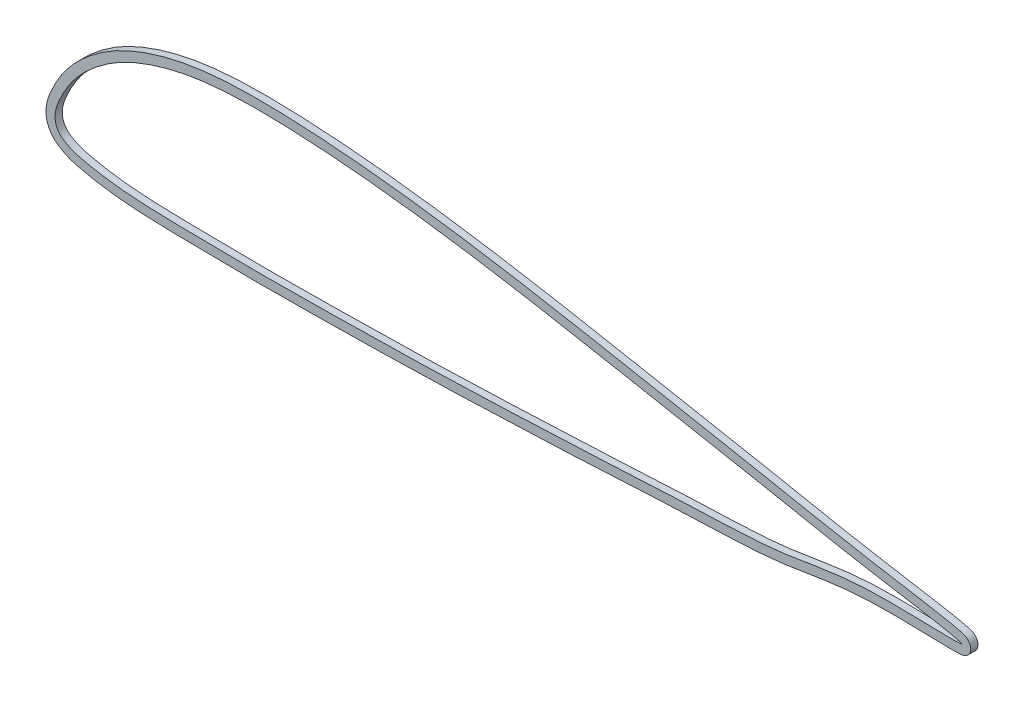
SolidWorks part; units mm, degrees
ref_plane "Front Plane" through (0, 0, 0) normal (0, 0, 1) x (1, 0, 0)
ref_plane "Top Plane" through (0, 0, 0) normal (0, 1, 0) x (1, 0, 0)
ref_plane "Right Plane" through (0, 0, 0) normal (1, 0, 0) x (0, 0, -1)
sketch "Sketch11" plane through (0, 0, 0) normal (0, 0, 1) x (1, 0, 0)
  line L0 (-43.8005, 0) -> (380.3083, 0) construction
  line L1 (0, 103.9604) -> (0, -61.3214) construction
  spline S0 degree 3 poles (5.2055, 33.3883) (8.3496, 38.4375) (12.1035, 43.4755) (16.9159, 48.515) (21.6177, 52.7069) (26.6422, 56.5456) (31.6627, 59.9068) (36.9892, 62.9567) (42.8619, 65.7826) (49.0168, 68.273) (55.4478, 70.4816) (61.4972, 72.2302) (68.0467, 73.8177) (74.3979, 75.051) (80.8825, 76.0083) (86.7438, 76.6697) (93.1859, 77.1993) (100.8735, 77.5954) (109.531, 77.773) (119.5404, 77.7056) (130.1167, 77.3864) (141.1364, 76.8376) (151.9182, 76.1212) (163.3231, 75.2) (175.9581, 73.987) (190.0575, 72.4145) (206.5823, 70.3225) (223.85, 67.8568) (240.4904, 65.2434) (253.8174, 63.0166) (268.6705, 60.4321) (285.232, 57.4255) (303.8938, 53.9257) (320.0111, 50.8601) (334.6114, 48.0737) (347.9319, 45.5391) (362.6553, 42.7654) (376.82, 40.1027) (391.3063, 37.3496) (404.1411, 34.8487) (419.3457, 31.8104) (436.364, 28.5258) (455.9997, 25.1096) (476.5677, 21.5774) (486.7341, 19.9981) (503.1995, 16.4828) (494.0454, 16.079) (487.8931, 16.3457) (477.383, 16.5668) (465.767, 16.8138) (452.7435, 16.8186) (439.1741, 16.1147) (425.2643, 14.4643) (412.0417, 12.2109) (396.9272, 9.9539) (381.3257, 8.8145) (365.9637, 8.1886) (351.799, 7.7061) (338.7226, 7.1495) (326.1387, 6.5056) (315.7861, 5.9505) (307.2533, 5.4916) (297.4115, 4.9796) (286.8565, 4.4714) (277.2883, 4.0439) (269.1855, 3.6963) (261.4554, 3.3751) (251.8585, 2.9904) (241.2598, 2.5754) (231.9793, 2.2273) (223.4506, 1.9259) (216.5377, 1.6954) (207.3161, 1.4113) (198.2656, 1.1695) (188.832, 0.9605) (181.1944, 0.8118) (173.3008, 0.675) (165.598, 0.5531) (157.1849, 0.4277) (148.2555, 0.2964) (137.6659, 0.1399) (127.333, 0.0247) (116.0359, -0.0123) (106.2761, 0.023) (96.7775, 0.1009) (88.6912, 0.1891) (80.0667, 0.3031) (71.5319, 0.4229) (61.8979, 0.5932) (53.0114, 0.8627) (44.0349, 1.3341) (36.2173, 1.9595) (28.3052, 2.9117) (21.1381, 4.1529) (14.9806, 5.476) (10.1274, 6.7093) (6.4953, 8.5231) (3.4169, 10.3581) (1.2362, 12.9218) (0.0423, 16.1496) (-0.1077, 19.6683) (0.8487, 24.1335) (2.8481, 28.6747) (5.2055, 33.3883) (8.3496, 38.4375) (12.1035, 43.4755) knots -0.015232 -0.009466 -0.004823 0 0.007707 0.013288 0.020114 0.025893 0.031552 0.037566 0.043618 0.050376 0.056746 0.063265 0.06857 0.076221 0.081956 0.087512 0.093268 0.100637 0.109759 0.118294 0.129567 0.14034 0.150184 0.160799 0.173412 0.186871 0.201804 0.221556 0.237286 0.250491 0.260611 0.280864 0.299143 0.315493 0.328286 0.342107 0.354686 0.371592 0.383765 0.397312 0.409372 0.428651 0.447018 0.468574 0.482905 0.490874 0.494014 0.502595 0.511845 0.523193 0.536597 0.549343 0.56248 0.577047 0.588116 0.606637 0.622219 0.632562 0.647602 0.66005 0.668982 0.677569 0.68475 0.697468 0.708114 0.712434 0.72091 0.730477 0.740196 0.751569 0.75732 0.764863 0.771562 0.783988 0.791033 0.798836 0.806068 0.813853 0.821103 0.830389 0.839665 0.851715 0.860257 0.872319 0.879926 0.887714 0.895694 0.904857 0.912386 0.923545 0.930552 0.938366 0.946209 0.953581 0.959372 0.964437 0.967975 0.971074 0.974748 0.97743 0.980891 0.984768 0.990534 0.995177 1 1.007707 1.013288 1.020114 only from (7.8664, 37.5601) to (7.8664, 37.5601)
sketch "Sketch14" plane through (0, 0, 0) normal (0, 0, 1) x (1, 0, 0)
  spline S1 degree 3 poles (12.1035, 43.4755) (8.3496, 38.4375) (5.2055, 33.3883) (2.8481, 28.6747) (0.8487, 24.1335) (-0.1077, 19.6683) (0.0423, 16.1496) (1.2362, 12.9218) (3.4169, 10.3581) (6.4953, 8.5231) (10.1274, 6.7093) (14.9806, 5.476) (21.1381, 4.1529) (28.3052, 2.9117) (36.2173, 1.9595) (44.0349, 1.3341) (53.0114, 0.8627) (61.8979, 0.5932) (71.5319, 0.4229) (80.0667, 0.3031) (88.6912, 0.1891) (96.7775, 0.1009) (106.2761, 0.023) (116.0359, -0.0123) (127.333, 0.0247) (137.6659, 0.1399) (148.2555, 0.2964) (157.1849, 0.4277) (165.598, 0.5531) (173.3008, 0.675) (181.1944, 0.8118) (188.832, 0.9605) (198.2656, 1.1695) (207.3161, 1.4113) (216.5377, 1.6954) (223.4506, 1.9259) (231.9793, 2.2273) (241.2598, 2.5754) (251.8585, 2.9904) (261.4554, 3.3751) (269.1855, 3.6963) (277.2883, 4.0439) (286.8565, 4.4714) (297.4115, 4.9796) (307.2533, 5.4916) (315.7861, 5.9505) (326.1387, 6.5056) (338.7226, 7.1495) (351.799, 7.7061) (365.9637, 8.1886) (381.3257, 8.8145) (396.9272, 9.9539) (412.0417, 12.2109) (425.2643, 14.4643) (439.1741, 16.1147) (452.7435, 16.8186) (465.767, 16.8138) (477.383, 16.5668) (487.8931, 16.3457) (494.0454, 16.079) (503.1995, 16.4828) (486.7341, 19.9981) (476.5677, 21.5774) (455.9997, 25.1096) (436.364, 28.5258) (419.3457, 31.8104) (404.1411, 34.8487) (391.3063, 37.3496) (376.82, 40.1027) (362.6553, 42.7654) (347.9319, 45.5391) (334.6114, 48.0737) (320.0111, 50.8601) (303.8938, 53.9257) (285.232, 57.4255) (268.6705, 60.4321) (253.8174, 63.0166) (240.4904, 65.2434) (223.85, 67.8568) (206.5823, 70.3225) (190.0575, 72.4145) (175.9581, 73.987) (163.3231, 75.2) (151.9182, 76.1212) (141.1364, 76.8376) (130.1167, 77.3864) (119.5404, 77.7056) (109.531, 77.773) (100.8735, 77.5954) (93.1859, 77.1993) (86.7438, 76.6697) (80.8825, 76.0083) (74.3979, 75.051) (68.0467, 73.8177) (61.4972, 72.2302) (55.4478, 70.4816) (49.0168, 68.273) (42.8619, 65.7826) (36.9892, 62.9567) (31.6627, 59.9068) (26.6422, 56.5456) (21.6177, 52.7069) (16.9159, 48.515) (12.1035, 43.4755) (8.3496, 38.4375) (5.2055, 33.3883) knots -0.020114 -0.013288 -0.007707 0 0.004823 0.009466 0.015232 0.019109 0.02257 0.025252 0.028926 0.032025 0.035563 0.040628 0.046419 0.053791 0.061634 0.069448 0.076455 0.087614 0.095143 0.104306 0.112286 0.120074 0.127681 0.139743 0.148285 0.160335 0.169611 0.178897 0.186147 0.193932 0.201164 0.208967 0.216012 0.228438 0.235137 0.24268 0.248431 0.259804 0.269523 0.27909 0.287566 0.291886 0.302532 0.31525 0.322431 0.331018 0.33995 0.352398 0.367438 0.377781 0.393363 0.411884 0.422953 0.43752 0.450657 0.463403 0.476807 0.488155 0.497405 0.505986 0.509126 0.517095 0.531426 0.552982 0.571349 0.590628 0.602688 0.616235 0.628408 0.645314 0.657893 0.671714 0.684507 0.700857 0.719136 0.739389 0.749509 0.762714 0.778444 0.798196 0.813129 0.826588 0.839201 0.849816 0.85966 0.870433 0.881706 0.890241 0.899363 0.906732 0.912488 0.918044 0.923779 0.93143 0.936735 0.943254 0.949624 0.956382 0.962434 0.968448 0.974107 0.979886 0.986712 0.992293 1 1.004823 1.009466 1.015232 only from (7.8664, 37.5601) to (7.8664, 37.5601) construction
  spline S2 degree 3 poles (486.9553, 11.3405) (489.0573, 11.2743) (490.4587, 11.2235) (493.2617, 11.1725) (494.6633, 11.1725) (496.766, 11.2157) (497.467, 11.2347) (498.5183, 11.2838) (498.8683, 11.3039) (499.567, 11.3593) (499.9156, 11.3943) (500.6097, 11.4977) (500.9555, 11.5671) (501.6286, 11.7618) (501.9597, 11.8887) (502.5839, 12.2003) (502.8785, 12.3844) (503.2927, 12.7052) (503.4269, 12.8203) (503.6811, 13.062) (503.8011, 13.1884) (504.1405, 13.584) (504.3394, 13.8693) (504.6797, 14.4852) (504.8164, 14.8077) (504.97, 15.3061) (505.0127, 15.4751) (505.0809, 15.8186) (505.1064, 15.9939) (505.1548, 16.5164) (505.151, 16.8641) (505.0721, 17.5581) (504.9957, 17.9049) (504.7772, 18.5657) (504.6349, 18.8838) (504.2823, 19.4946) (504.078, 19.7769) (503.6166, 20.2982) (503.3564, 20.539) (502.8006, 20.9635) (502.505, 21.148) (501.8847, 21.4715) (501.5604, 21.6101) (500.9082, 21.8543) (500.5781, 21.9615) (499.9139, 22.1614) (499.5797, 22.2539) (498.574, 22.5192) (497.8991, 22.68) (496.5459, 22.989) (495.8674, 23.1366) (493.8292, 23.5687) (492.4682, 23.8444) (489.7446, 24.3875) (488.3817, 24.6522) (485.6521, 25.1617) (484.2854, 25.4058) (481.5483, 25.8729) (480.1779, 26.0959) (473.3265, 27.2155) (467.8525, 28.1508) (459.6429, 29.5619) (456.9068, 30.0343) (451.435, 30.9819) (448.6995, 31.4578) (443.2309, 32.4229) (440.4978, 32.9121) (435.0356, 33.9124) (432.3065, 34.4234) (424.1236, 35.9808) (418.6745, 37.0528) (410.5033, 38.6746) (407.7797, 39.2164) (402.3311, 40.2913) (399.6061, 40.8246) (385.9774, 43.4713) (375.062, 45.5195) (358.6904, 48.6003) (353.2334, 49.6276) (342.3215, 51.6954) (336.8665, 52.7349) (320.5021, 55.8553) (309.5931, 57.9389) (287.7626, 62.0371) (276.8411, 64.0508) (254.9679, 67.9098) (244.0159, 69.7531) (222.0652, 73.1792) (211.0654, 74.7634) (189.0115, 77.5957) (177.975, 78.8412) (161.4015, 80.3747) (155.8738, 80.83) (144.8115, 81.6161) (139.2768, 81.9456) (128.1987, 82.4515) (122.6556, 82.6318) (111.5573, 82.7783) (106.0019, 82.7411) (97.655, 82.4373) (94.8688, 82.295) (89.2971, 81.9069) (86.5233, 81.662) (81.0041, 81.052) (78.2588, 80.6868) (72.8008, 79.8186) (70.0883, 79.3149) (62.0027, 77.585) (56.6811, 76.1415) (48.814, 73.4896) (46.2106, 72.5256) (42.3394, 70.9366) (41.0548, 70.3826) (38.4986, 69.2195) (37.2298, 68.6114) (33.4819, 66.713) (31.0526, 65.3419) (26.3335, 62.387) (24.0423, 60.8056) (20.7015, 58.2872) (19.6045, 57.4224) (17.9858, 56.0845) (17.4507, 55.6317) (16.3896, 54.7123) (15.863, 54.2449) (14.304, 52.8274) (13.2916, 51.8619) (11.324, 49.8871) (10.3698, 48.8771) (7.615, 45.7646) (5.9292, 43.5745) (3.5741, 40.1567) (2.8158, 38.997) (1.3671, 36.6257) (0.6801, 35.4116) (-0.6179, 32.9251) (-1.2353, 31.6543) (-2.4154, 29.1008) (-2.9693, 27.8117) (-3.9165, 25.1786) (-4.3117, 23.8352) (-4.6559, 22.1048) (-4.7172, 21.7561) (-4.8232, 21.0531) (-4.8679, 20.6978) (-4.9736, 19.6342) (-5.0069, 18.9258) (-4.9908, 17.5109) (-4.9415, 16.8043) (-4.7965, 15.7458) (-4.736, 15.3918) (-4.5912, 14.6934) (-4.5069, 14.3486) (-4.2191, 13.3276) (-3.9808, 12.6644) (-3.5519, 11.6966) (-3.397, 11.3785) (-3.0623, 10.7516) (-2.8818, 10.4417) (-2.3081, 9.5354) (-1.8859, 8.9656) (-0.9678, 7.8897) (-0.472, 7.3837) (0.3275, 6.6726) (0.604, 6.4433) (1.1672, 6.007) (1.4546, 5.7989) (2.3314, 5.2002) (2.9356, 4.8352) (4.1646, 4.1412) (4.787, 3.8078) (6.051, 3.1748) (6.6933, 2.8761) (8.0059, 2.3276) (8.6693, 2.0826) (10.0038, 1.6414) (10.6754, 1.4442) (12.0244, 1.0801) (12.7018, 0.9133) (14.0586, 0.5911) (14.738, 0.4348) (16.7784, -0.0209) (18.1421, -0.307) (22.2423, -1.1159) (24.9881, -1.5899) (30.5071, -2.3922) (33.2801, -2.7213) (38.8468, -3.2696) (41.6379, -3.4885) (47.2152, -3.8453) (50.0043, -3.9837) (58.3725, -4.3242) (63.9524, -4.4468) (72.3228, -4.5867) (75.113, -4.6275) (80.6935, -4.7052) (83.4837, -4.7429) (97.435, -4.9195) (108.5966, -5.0198) (125.3409, -4.9853) (130.9228, -4.9377) (142.0869, -4.7992) (147.6692, -4.713) (164.4159, -4.466) (175.5807, -4.3036) (192.3232, -3.9678) (197.9033, -3.8398) (209.0613, -3.54) (214.6393, -3.3694) (231.3712, -2.8129) (242.523, -2.3835) (264.8251, -1.4963) (275.9752, -1.0327) (292.6964, -0.2556) (298.2695, 0.0181) (309.4139, 0.5979) (314.9855, 0.9013) (326.1293, 1.4962) (331.7014, 1.789) (342.8482, 2.3211) (348.4229, 2.5592) (359.5754, 2.975) (365.1528, 3.1566) (373.5154, 3.5041) (376.3024, 3.6318) (381.8744, 3.9264) (384.6595, 4.0924) (390.2265, 4.491) (393.0084, 4.7236) (397.1777, 5.1454) (398.5669, 5.2982) (401.3439, 5.6317) (402.7317, 5.8126) (406.8936, 6.3878) (409.6661, 6.8147) (415.2095, 7.6995) (417.9805, 8.157) (423.5244, 9.0349) (426.2972, 9.4536) (431.8478, 10.1927) (434.6252, 10.5166) (440.1856, 11.0523) (442.9686, 11.2612) (448.5399, 11.571) (451.3281, 11.6728) (459.6991, 11.8469) (465.2879, 11.7938) (473.6745, 11.6461) (476.4705, 11.5856) (480.6645, 11.4965) (482.0626, 11.4662) (484.1598, 11.4159) (484.859, 11.3983) (486.2574, 11.3605) (486.9553, 11.3405) (489.0573, 11.2743) (490.4587, 11.2235) knots -0.001953 -0.001953 0 0 0.003906 0.003906 0.007813 0.007813 0.009766 0.009766 0.010742 0.010742 0.011719 0.011719 0.012695 0.012695 0.013672 0.013672 0.014648 0.014648 0.015137 0.015137 0.015625 0.015625 0.016602 0.016602 0.017578 0.017578 0.018066 0.018066 0.018555 0.018555 0.019531 0.019531 0.020508 0.020508 0.021484 0.021484 0.022461 0.022461 0.023438 0.023438 0.024414 0.024414 0.025391 0.025391 0.026367 0.026367 0.027344 0.027344 0.029297 0.029297 0.03125 0.03125 0.035156 0.035156 0.039063 0.039063 0.042969 0.042969 0.046875 0.046875 0.0625 0.0625 0.070313 0.070313 0.078125 0.078125 0.085938 0.085938 0.09375 0.09375 0.109375 0.109375 0.117188 0.117188 0.125 0.125 0.15625 0.15625 0.171875 0.171875 0.1875 0.1875 0.21875 0.21875 0.25 0.25 0.28125 0.28125 0.3125 0.3125 0.34375 0.34375 0.359375 0.359375 0.375 0.375 0.390625 0.390625 0.40625 0.40625 0.414063 0.414063 0.421875 0.421875 0.429688 0.429688 0.4375 0.4375 0.453125 0.453125 0.460938 0.460938 0.464844 0.464844 0.46875 0.46875 0.476563 0.476563 0.484375 0.484375 0.488281 0.488281 0.490234 0.490234 0.492188 0.492188 0.496094 0.496094 0.5 0.5 0.507813 0.507813 0.511719 0.511719 0.515625 0.515625 0.519531 0.519531 0.523438 0.523438 0.527344 0.527344 0.52832 0.52832 0.529297 0.529297 0.53125 0.53125 0.533203 0.533203 0.53418 0.53418 0.535156 0.535156 0.537109 0.537109 0.538086 0.538086 0.539063 0.539063 0.541016 0.541016 0.542969 0.542969 0.543945 0.543945 0.544922 0.544922 0.546875 0.546875 0.548828 0.548828 0.550781 0.550781 0.552734 0.552734 0.554688 0.554688 0.556641 0.556641 0.558594 0.558594 0.5625 0.5625 0.570313 0.570313 0.578125 0.578125 0.585938 0.585938 0.59375 0.59375 0.609375 0.609375 0.617188 0.617188 0.625 0.625 0.65625 0.65625 0.671875 0.671875 0.6875 0.6875 0.71875 0.71875 0.734375 0.734375 0.75 0.75 0.78125 0.78125 0.8125 0.8125 0.828125 0.828125 0.84375 0.84375 0.859375 0.859375 0.875 0.875 0.890625 0.890625 0.898438 0.898438 0.90625 0.90625 0.914063 0.914063 0.917969 0.917969 0.921875 0.921875 0.929688 0.929688 0.9375 0.9375 0.945313 0.945313 0.953125 0.953125 0.960938 0.960938 0.96875 0.96875 0.984375 0.984375 0.992188 0.992188 0.996094 0.996094 0.998047 0.998047 1 1 1.003906 1.003906 1.007813 only from (487.656, 11.3184) to (487.656, 11.3184)
  spline S3 degree 3 poles (486.9553, 11.3405) (489.0573, 11.2743) (490.4587, 11.2235) (493.2617, 11.1725) (494.6633, 11.1725) (496.766, 11.2157) (497.467, 11.2347) (498.5183, 11.2838) (498.8683, 11.3039) (499.567, 11.3593) (499.9156, 11.3943) (500.6097, 11.4977) (500.9555, 11.5671) (501.6286, 11.7618) (501.9597, 11.8887) (502.5839, 12.2003) (502.8785, 12.3844) (503.2927, 12.7052) (503.4269, 12.8203) (503.6811, 13.062) (503.8011, 13.1884) (504.1405, 13.584) (504.3394, 13.8693) (504.6797, 14.4852) (504.8164, 14.8077) (504.97, 15.3061) (505.0127, 15.4751) (505.0809, 15.8186) (505.1064, 15.9939) (505.1548, 16.5164) (505.151, 16.8641) (505.0721, 17.5581) (504.9957, 17.9049) (504.7772, 18.5657) (504.6349, 18.8838) (504.2823, 19.4946) (504.078, 19.7769) (503.6166, 20.2982) (503.3564, 20.539) (502.8006, 20.9635) (502.505, 21.148) (501.8847, 21.4715) (501.5604, 21.6101) (500.9082, 21.8543) (500.5781, 21.9615) (499.9139, 22.1614) (499.5797, 22.2539) (498.574, 22.5192) (497.8991, 22.68) (496.5459, 22.989) (495.8674, 23.1366) (493.8292, 23.5687) (492.4682, 23.8444) (489.7446, 24.3875) (488.3817, 24.6522) (485.6521, 25.1617) (484.2854, 25.4058) (481.5483, 25.8729) (480.1779, 26.0959) (473.3265, 27.2155) (467.8525, 28.1508) (459.6429, 29.5619) (456.9068, 30.0343) (451.435, 30.9819) (448.6995, 31.4578) (443.2309, 32.4229) (440.4978, 32.9121) (435.0356, 33.9124) (432.3065, 34.4234) (424.1236, 35.9808) (418.6745, 37.0528) (410.5033, 38.6746) (407.7797, 39.2164) (402.3311, 40.2913) (399.6061, 40.8246) (385.9774, 43.4713) (375.062, 45.5195) (358.6904, 48.6003) (353.2334, 49.6276) (342.3215, 51.6954) (336.8665, 52.7349) (320.5021, 55.8553) (309.5931, 57.9389) (287.7626, 62.0371) (276.8411, 64.0508) (254.9679, 67.9098) (244.0159, 69.7531) (222.0652, 73.1792) (211.0654, 74.7634) (189.0115, 77.5957) (177.975, 78.8412) (161.4015, 80.3747) (155.8738, 80.83) (144.8115, 81.6161) (139.2768, 81.9456) (128.1987, 82.4515) (122.6556, 82.6318) (111.5573, 82.7783) (106.0019, 82.7411) (97.655, 82.4373) (94.8688, 82.295) (89.2971, 81.9069) (86.5233, 81.662) (81.0041, 81.052) (78.2588, 80.6868) (72.8008, 79.8186) (70.0883, 79.3149) (62.0027, 77.585) (56.6811, 76.1415) (48.814, 73.4896) (46.2106, 72.5256) (42.3394, 70.9366) (41.0548, 70.3826) (38.4986, 69.2195) (37.2298, 68.6114) (33.4819, 66.713) (31.0526, 65.3419) (26.3335, 62.387) (24.0423, 60.8056) (20.7015, 58.2872) (19.6045, 57.4224) (17.9858, 56.0845) (17.4507, 55.6317) (16.3896, 54.7123) (15.863, 54.2449) (14.304, 52.8274) (13.2916, 51.8619) (11.324, 49.8871) (10.3698, 48.8771) (7.615, 45.7646) (5.9292, 43.5745) (3.5741, 40.1567) (2.8158, 38.997) (1.3671, 36.6257) (0.6801, 35.4116) (-0.6179, 32.9251) (-1.2353, 31.6543) (-2.4154, 29.1008) (-2.9693, 27.8117) (-3.9165, 25.1786) (-4.3117, 23.8352) (-4.6559, 22.1048) (-4.7172, 21.7561) (-4.8232, 21.0531) (-4.8679, 20.6978) (-4.9736, 19.6342) (-5.0069, 18.9258) (-4.9908, 17.5109) (-4.9415, 16.8043) (-4.7965, 15.7458) (-4.736, 15.3918) (-4.5912, 14.6934) (-4.5069, 14.3486) (-4.2191, 13.3276) (-3.9808, 12.6644) (-3.5519, 11.6966) (-3.397, 11.3785) (-3.0623, 10.7516) (-2.8818, 10.4417) (-2.3081, 9.5354) (-1.8859, 8.9656) (-0.9678, 7.8897) (-0.472, 7.3837) (0.3275, 6.6726) (0.604, 6.4433) (1.1672, 6.007) (1.4546, 5.7989) (2.3314, 5.2002) (2.9356, 4.8352) (4.1646, 4.1412) (4.787, 3.8078) (6.051, 3.1748) (6.6933, 2.8761) (8.0059, 2.3276) (8.6693, 2.0826) (10.0038, 1.6414) (10.6754, 1.4442) (12.0244, 1.0801) (12.7018, 0.9133) (14.0586, 0.5911) (14.738, 0.4348) (16.7784, -0.0209) (18.1421, -0.307) (22.2423, -1.1159) (24.9881, -1.5899) (30.5071, -2.3922) (33.2801, -2.7213) (38.8468, -3.2696) (41.6379, -3.4885) (47.2152, -3.8453) (50.0043, -3.9837) (58.3725, -4.3242) (63.9524, -4.4468) (72.3228, -4.5867) (75.113, -4.6275) (80.6935, -4.7052) (83.4837, -4.7429) (97.435, -4.9195) (108.5966, -5.0198) (125.3409, -4.9853) (130.9228, -4.9377) (142.0869, -4.7992) (147.6692, -4.713) (164.4159, -4.466) (175.5807, -4.3036) (192.3232, -3.9678) (197.9033, -3.8398) (209.0613, -3.54) (214.6393, -3.3694) (231.3712, -2.8129) (242.523, -2.3835) (264.8251, -1.4963) (275.9752, -1.0327) (292.6964, -0.2556) (298.2695, 0.0181) (309.4139, 0.5979) (314.9855, 0.9013) (326.1293, 1.4962) (331.7014, 1.789) (342.8482, 2.3211) (348.4229, 2.5592) (359.5754, 2.975) (365.1528, 3.1566) (373.5154, 3.5041) (376.3024, 3.6318) (381.8744, 3.9264) (384.6595, 4.0924) (390.2265, 4.491) (393.0084, 4.7236) (397.1777, 5.1454) (398.5669, 5.2982) (401.3439, 5.6317) (402.7317, 5.8126) (406.8936, 6.3878) (409.6661, 6.8147) (415.2095, 7.6995) (417.9805, 8.157) (423.5244, 9.0349) (426.2972, 9.4536) (431.8478, 10.1927) (434.6252, 10.5166) (440.1856, 11.0523) (442.9686, 11.2612) (448.5399, 11.571) (451.3281, 11.6728) (459.6991, 11.8469) (465.2879, 11.7938) (473.6745, 11.6461) (476.4705, 11.5856) (480.6645, 11.4965) (482.0626, 11.4662) (484.1598, 11.4159) (484.859, 11.3983) (486.2574, 11.3605) (486.9553, 11.3405) (489.0573, 11.2743) (490.4587, 11.2235) knots -0.001953 -0.001953 0 0 0.003906 0.003906 0.007813 0.007813 0.009766 0.009766 0.010742 0.010742 0.011719 0.011719 0.012695 0.012695 0.013672 0.013672 0.014648 0.014648 0.015137 0.015137 0.015625 0.015625 0.016602 0.016602 0.017578 0.017578 0.018066 0.018066 0.018555 0.018555 0.019531 0.019531 0.020508 0.020508 0.021484 0.021484 0.022461 0.022461 0.023438 0.023438 0.024414 0.024414 0.025391 0.025391 0.026367 0.026367 0.027344 0.027344 0.029297 0.029297 0.03125 0.03125 0.035156 0.035156 0.039063 0.039063 0.042969 0.042969 0.046875 0.046875 0.0625 0.0625 0.070313 0.070313 0.078125 0.078125 0.085938 0.085938 0.09375 0.09375 0.109375 0.109375 0.117188 0.117188 0.125 0.125 0.15625 0.15625 0.171875 0.171875 0.1875 0.1875 0.21875 0.21875 0.25 0.25 0.28125 0.28125 0.3125 0.3125 0.34375 0.34375 0.359375 0.359375 0.375 0.375 0.390625 0.390625 0.40625 0.40625 0.414063 0.414063 0.421875 0.421875 0.429688 0.429688 0.4375 0.4375 0.453125 0.453125 0.460938 0.460938 0.464844 0.464844 0.46875 0.46875 0.476563 0.476563 0.484375 0.484375 0.488281 0.488281 0.490234 0.490234 0.492188 0.492188 0.496094 0.496094 0.5 0.5 0.507813 0.507813 0.511719 0.511719 0.515625 0.515625 0.519531 0.519531 0.523438 0.523438 0.527344 0.527344 0.52832 0.52832 0.529297 0.529297 0.53125 0.53125 0.533203 0.533203 0.53418 0.53418 0.535156 0.535156 0.537109 0.537109 0.538086 0.538086 0.539063 0.539063 0.541016 0.541016 0.542969 0.542969 0.543945 0.543945 0.544922 0.544922 0.546875 0.546875 0.548828 0.548828 0.550781 0.550781 0.552734 0.552734 0.554688 0.554688 0.556641 0.556641 0.558594 0.558594 0.5625 0.5625 0.570313 0.570313 0.578125 0.578125 0.585938 0.585938 0.59375 0.59375 0.609375 0.609375 0.617188 0.617188 0.625 0.625 0.65625 0.65625 0.671875 0.671875 0.6875 0.6875 0.71875 0.71875 0.734375 0.734375 0.75 0.75 0.78125 0.78125 0.8125 0.8125 0.828125 0.828125 0.84375 0.84375 0.859375 0.859375 0.875 0.875 0.890625 0.890625 0.898438 0.898438 0.90625 0.90625 0.914063 0.914063 0.917969 0.917969 0.921875 0.921875 0.929688 0.929688 0.9375 0.9375 0.945313 0.945313 0.953125 0.953125 0.960938 0.960938 0.96875 0.96875 0.984375 0.984375 0.992188 0.992188 0.996094 0.996094 0.998047 0.998047 1 1 1.003906 1.003906 1.007813 only from (487.656, 11.3184) to (487.656, 11.3184)
  spline S4 degree 3 poles (12.1035, 43.4755) (8.3496, 38.4375) (5.2055, 33.3883) (2.8481, 28.6747) (0.8487, 24.1335) (-0.1077, 19.6683) (0.0423, 16.1496) (1.2362, 12.9218) (3.4169, 10.3581) (6.4953, 8.5231) (10.1274, 6.7093) (14.9806, 5.476) (21.1381, 4.1529) (28.3052, 2.9117) (36.2173, 1.9595) (44.0349, 1.3341) (53.0114, 0.8627) (61.8979, 0.5932) (71.5319, 0.4229) (80.0667, 0.3031) (88.6912, 0.1891) (96.7775, 0.1009) (106.2761, 0.023) (116.0359, -0.0123) (127.333, 0.0247) (137.6659, 0.1399) (148.2555, 0.2964) (157.1849, 0.4277) (165.598, 0.5531) (173.3008, 0.675) (181.1944, 0.8118) (188.832, 0.9605) (198.2656, 1.1695) (207.3161, 1.4113) (216.5377, 1.6954) (223.4506, 1.9259) (231.9793, 2.2273) (241.2598, 2.5754) (251.8585, 2.9904) (261.4554, 3.3751) (269.1855, 3.6963) (277.2883, 4.0439) (286.8565, 4.4714) (297.4115, 4.9796) (307.2533, 5.4916) (315.7861, 5.9505) (326.1387, 6.5056) (338.7226, 7.1495) (351.799, 7.7061) (365.9637, 8.1886) (381.3257, 8.8145) (396.9272, 9.9539) (412.0417, 12.2109) (425.2643, 14.4643) (439.1741, 16.1147) (452.7435, 16.8186) (465.767, 16.8138) (477.383, 16.5668) (487.8931, 16.3457) (494.0454, 16.079) (503.1995, 16.4828) (486.7341, 19.9981) (476.5677, 21.5774) (455.9997, 25.1096) (436.364, 28.5258) (419.3457, 31.8104) (404.1411, 34.8487) (391.3063, 37.3496) (376.82, 40.1027) (362.6553, 42.7654) (347.9319, 45.5391) (334.6114, 48.0737) (320.0111, 50.8601) (303.8938, 53.9257) (285.232, 57.4255) (268.6705, 60.4321) (253.8174, 63.0166) (240.4904, 65.2434) (223.85, 67.8568) (206.5823, 70.3225) (190.0575, 72.4145) (175.9581, 73.987) (163.3231, 75.2) (151.9182, 76.1212) (141.1364, 76.8376) (130.1167, 77.3864) (119.5404, 77.7056) (109.531, 77.773) (100.8735, 77.5954) (93.1859, 77.1993) (86.7438, 76.6697) (80.8825, 76.0083) (74.3979, 75.051) (68.0467, 73.8177) (61.4972, 72.2302) (55.4478, 70.4816) (49.0168, 68.273) (42.8619, 65.7826) (36.9892, 62.9567) (31.6627, 59.9068) (26.6422, 56.5456) (21.6177, 52.7069) (16.9159, 48.515) (12.1035, 43.4755) (8.3496, 38.4375) (5.2055, 33.3883) knots -0.020114 -0.013288 -0.007707 0 0.004823 0.009466 0.015232 0.019109 0.02257 0.025252 0.028926 0.032025 0.035563 0.040628 0.046419 0.053791 0.061634 0.069448 0.076455 0.087614 0.095143 0.104306 0.112286 0.120074 0.127681 0.139743 0.148285 0.160335 0.169611 0.178897 0.186147 0.193932 0.201164 0.208967 0.216012 0.228438 0.235137 0.24268 0.248431 0.259804 0.269523 0.27909 0.287566 0.291886 0.302532 0.31525 0.322431 0.331018 0.33995 0.352398 0.367438 0.377781 0.393363 0.411884 0.422953 0.43752 0.450657 0.463403 0.476807 0.488155 0.497405 0.505986 0.509126 0.517095 0.531426 0.552982 0.571349 0.590628 0.602688 0.616235 0.628408 0.645314 0.657893 0.671714 0.684507 0.700857 0.719136 0.739389 0.749509 0.762714 0.778444 0.798196 0.813129 0.826588 0.839201 0.849816 0.85966 0.870433 0.881706 0.890241 0.899363 0.906732 0.912488 0.918044 0.923779 0.93143 0.936735 0.943254 0.949624 0.956382 0.962434 0.968448 0.974107 0.979886 0.986712 0.992293 1 1.004823 1.009466 1.015232 only from (7.8664, 37.5601) to (7.8664, 37.5601)
  dimension "D1" = 5
extrude "Boss-Extrude5" add sketch "Sketch14" along normal blind 4 contours S3 S4
sketch "Sketch15" plane through (0, 0, 4) normal (0, 0, 1) x (1, 0, 0)
  line L0 (82.4618, 35.8287) -> (116.17, 35.8287) construction
  line L1 (299.0602, 54.8287) -> (24.4221, 54.8287) construction
  line L2 (355.1442, 7.8128) -> (355.1442, 44.1809) construction
  line L3 (116.17, 35.8287) -> (100.4588, 35.8287) construction
  line L4 (244.4964, 2.7032) -> (244.4964, 64.5645) construction
  line L5 (149.087, 0.3085) -> (149.087, 76.2991) construction
  line L6 (246.4964, 52.8287) -> (309.6489, 52.8287)
  line L7 (27.1468, 56.8287) -> (71.1553, 56.8287)
  line L8 (61.4618, 0.6248) -> (61.4618, 72.1745)
  line L9 (65.4618, 73.1794) -> (65.4618, 0.535)
  line L10 (71.1553, 56.8287) -> (142.087, 56.8287)
  line L11 (147.087, 61.8287) -> (147.087, 76.4358)
  line L12 (151.087, 76.1567) -> (151.087, 61.8287)
  line L13 (156.087, 56.8287) -> (242.4964, 56.8287)
  line L14 (242.4964, 56.8287) -> (242.4964, 64.8924)
  line L15 (246.4964, 56.8287) -> (288.3526, 56.8287)
  line L16 (242.4964, 52.8287) -> (242.4964, 2.6259)
  line L17 (246.4964, 56.8287) -> (246.4964, 64.234)
  line L18 (357.1442, 43.804) -> (357.1442, 7.8851)
  line L19 (353.1442, 7.7386) -> (353.1442, 44.5581)
  line L20 (151.087, 0.338) -> (151.087, 47.8287)
  line L21 (156.087, 52.8287) -> (242.4964, 52.8287)
  line L22 (142.087, 52.8287) -> (21.8954, 52.8287)
  line L23 (505.1442, 89.3367) -> (505.1442, -11.9293) construction
  line L24 (147.087, 47.8287) -> (147.087, 0.2791)
  line L25 (246.4964, 52.8287) -> (246.4964, 2.781)
  line L26 (63.4618, 72.6923) -> (63.4618, 0.5773) construction
  circle A0 centre (82.4618, 35.8287) radius 17
  circle A1 centre (82.4618, 35.8287) radius 13
  arc A2 (151.087, 61.8287) -> (156.087, 56.8287) centre (156.087, 61.8287) ccw
  arc A3 (142.087, 56.8287) -> (147.087, 61.8287) centre (142.087, 61.8287) ccw
  arc A4 (142.087, 52.8287) -> (147.087, 47.8287) centre (142.087, 47.8287) cw
  arc A5 (151.087, 47.8287) -> (156.087, 52.8287) centre (156.087, 47.8287) cw
  spline S0 degree 3 poles (12.1035, 43.4755) (8.3496, 38.4375) (5.2055, 33.3883) (2.8481, 28.6747) (0.8487, 24.1335) (-0.1077, 19.6683) (0.0423, 16.1496) (1.2362, 12.9218) (3.4169, 10.3581) (6.4953, 8.5231) (10.1274, 6.7093) (14.9806, 5.476) (21.1381, 4.1529) (28.3052, 2.9117) (36.2173, 1.9595) (44.0349, 1.3341) (53.0114, 0.8627) (61.8979, 0.5932) (71.5319, 0.4229) (80.0667, 0.3031) (88.6912, 0.1891) (96.7775, 0.1009) (106.2761, 0.023) (116.0359, -0.0123) (127.333, 0.0247) (137.6659, 0.1399) (148.2555, 0.2964) (157.1849, 0.4277) (165.598, 0.5531) (173.3008, 0.675) (181.1944, 0.8118) (188.832, 0.9605) (198.2656, 1.1695) (207.3161, 1.4113) (216.5377, 1.6954) (223.4506, 1.9259) (231.9793, 2.2273) (241.2598, 2.5754) (251.8585, 2.9904) (261.4554, 3.3751) (269.1855, 3.6963) (277.2883, 4.0439) (286.8565, 4.4714) (297.4115, 4.9796) (307.2533, 5.4916) (315.7861, 5.9505) (326.1387, 6.5056) (338.7226, 7.1495) (351.799, 7.7061) (365.9637, 8.1886) (381.3257, 8.8145) (396.9272, 9.9539) (412.0417, 12.2109) (425.2643, 14.4643) (439.1741, 16.1147) (452.7435, 16.8186) (465.767, 16.8138) (477.383, 16.5668) (487.8931, 16.3457) (494.0454, 16.079) (503.1995, 16.4828) (486.7341, 19.9981) (476.5677, 21.5774) (455.9997, 25.1096) (436.364, 28.5258) (419.3457, 31.8104) (404.1411, 34.8487) (391.3063, 37.3496) (376.82, 40.1027) (362.6553, 42.7654) (347.9319, 45.5391) (334.6114, 48.0737) (320.0111, 50.8601) (303.8938, 53.9257) (285.232, 57.4255) (268.6705, 60.4321) (253.8174, 63.0166) (240.4904, 65.2434) (223.85, 67.8568) (206.5823, 70.3225) (190.0575, 72.4145) (175.9581, 73.987) (163.3231, 75.2) (151.9182, 76.1212) (141.1364, 76.8376) (130.1167, 77.3864) (119.5404, 77.7056) (109.531, 77.773) (100.8735, 77.5954) (93.1859, 77.1993) (86.7438, 76.6697) (80.8825, 76.0083) (74.3979, 75.051) (68.0467, 73.8177) (61.4972, 72.2302) (55.4478, 70.4816) (49.0168, 68.273) (42.8619, 65.7826) (36.9892, 62.9567) (31.6627, 59.9068) (26.6422, 56.5456) (21.6177, 52.7069) (16.9159, 48.515) (12.1035, 43.4755) (8.3496, 38.4375) (5.2055, 33.3883) knots -0.020114 -0.013288 -0.007707 0 0.004823 0.009466 0.015232 0.019109 0.02257 0.025252 0.028926 0.032025 0.035563 0.040628 0.046419 0.053791 0.061634 0.069448 0.076455 0.087614 0.095143 0.104306 0.112286 0.120074 0.127681 0.139743 0.148285 0.160335 0.169611 0.178897 0.186147 0.193932 0.201164 0.208967 0.216012 0.228438 0.235137 0.24268 0.248431 0.259804 0.269523 0.27909 0.287566 0.291886 0.302532 0.31525 0.322431 0.331018 0.33995 0.352398 0.367438 0.377781 0.393363 0.411884 0.422953 0.43752 0.450657 0.463403 0.476807 0.488155 0.497405 0.505986 0.509126 0.517095 0.531426 0.552982 0.571349 0.590628 0.602688 0.616235 0.628408 0.645314 0.657893 0.671714 0.684507 0.700857 0.719136 0.739389 0.749509 0.762714 0.778444 0.798196 0.813129 0.826588 0.839201 0.849816 0.85966 0.870433 0.881706 0.890241 0.899363 0.906732 0.912488 0.918044 0.923779 0.93143 0.936735 0.943254 0.949624 0.956382 0.962434 0.968448 0.974107 0.979886 0.986712 0.992293 1 1.004823 1.009466 1.015232 only from (7.8664, 37.5601) to (7.8664, 37.5601) construction
  spline S1 degree 3 poles (12.1035, 43.4755) (8.3496, 38.4375) (5.2055, 33.3883) (2.8481, 28.6747) (0.8487, 24.1335) (-0.1077, 19.6683) (0.0423, 16.1496) (1.2362, 12.9218) (3.4169, 10.3581) (6.4953, 8.5231) (10.1274, 6.7093) (14.9806, 5.476) (21.1381, 4.1529) (28.3052, 2.9117) (36.2173, 1.9595) (44.0349, 1.3341) (53.0114, 0.8627) (61.8979, 0.5932) (71.5319, 0.4229) (80.0667, 0.3031) (88.6912, 0.1891) (96.7775, 0.1009) (106.2761, 0.023) (116.0359, -0.0123) (127.333, 0.0247) (137.6659, 0.1399) (148.2555, 0.2964) (157.1849, 0.4277) (165.598, 0.5531) (173.3008, 0.675) (181.1944, 0.8118) (188.832, 0.9605) (198.2656, 1.1695) (207.3161, 1.4113) (216.5377, 1.6954) (223.4506, 1.9259) (231.9793, 2.2273) (241.2598, 2.5754) (251.8585, 2.9904) (261.4554, 3.3751) (269.1855, 3.6963) (277.2883, 4.0439) (286.8565, 4.4714) (297.4115, 4.9796) (307.2533, 5.4916) (315.7861, 5.9505) (326.1387, 6.5056) (338.7226, 7.1495) (351.799, 7.7061) (365.9637, 8.1886) (381.3257, 8.8145) (396.9272, 9.9539) (412.0417, 12.2109) (425.2643, 14.4643) (439.1741, 16.1147) (452.7435, 16.8186) (465.767, 16.8138) (477.383, 16.5668) (487.8931, 16.3457) (494.0454, 16.079) (503.1995, 16.4828) (486.7341, 19.9981) (476.5677, 21.5774) (455.9997, 25.1096) (436.364, 28.5258) (419.3457, 31.8104) (404.1411, 34.8487) (391.3063, 37.3496) (376.82, 40.1027) (362.6553, 42.7654) (347.9319, 45.5391) (334.6114, 48.0737) (320.0111, 50.8601) (303.8938, 53.9257) (285.232, 57.4255) (268.6705, 60.4321) (253.8174, 63.0166) (240.4904, 65.2434) (223.85, 67.8568) (206.5823, 70.3225) (190.0575, 72.4145) (175.9581, 73.987) (163.3231, 75.2) (151.9182, 76.1212) (141.1364, 76.8376) (130.1167, 77.3864) (119.5404, 77.7056) (109.531, 77.773) (100.8735, 77.5954) (93.1859, 77.1993) (86.7438, 76.6697) (80.8825, 76.0083) (74.3979, 75.051) (68.0467, 73.8177) (61.4972, 72.2302) (55.4478, 70.4816) (49.0168, 68.273) (42.8619, 65.7826) (36.9892, 62.9567) (31.6627, 59.9068) (26.6422, 56.5456) (21.6177, 52.7069) (16.9159, 48.515) (12.1035, 43.4755) (8.3496, 38.4375) (5.2055, 33.3883) knots -0.020114 -0.013288 -0.007707 0 0.004823 0.009466 0.015232 0.019109 0.02257 0.025252 0.028926 0.032025 0.035563 0.040628 0.046419 0.053791 0.061634 0.069448 0.076455 0.087614 0.095143 0.104306 0.112286 0.120074 0.127681 0.139743 0.148285 0.160335 0.169611 0.178897 0.186147 0.193932 0.201164 0.208967 0.216012 0.228438 0.235137 0.24268 0.248431 0.259804 0.269523 0.27909 0.287566 0.291886 0.302532 0.31525 0.322431 0.331018 0.33995 0.352398 0.367438 0.377781 0.393363 0.411884 0.422953 0.43752 0.450657 0.463403 0.476807 0.488155 0.497405 0.505986 0.509126 0.517095 0.531426 0.552982 0.571349 0.590628 0.602688 0.616235 0.628408 0.645314 0.657893 0.671714 0.684507 0.700857 0.719136 0.739389 0.749509 0.762714 0.778444 0.798196 0.813129 0.826588 0.839201 0.849816 0.85966 0.870433 0.881706 0.890241 0.899363 0.906732 0.912488 0.918044 0.923779 0.93143 0.936735 0.943254 0.949624 0.956382 0.962434 0.968448 0.974107 0.979886 0.986712 0.992293 1 1.004823 1.009466 1.015232 only from (7.8664, 37.5601) to (7.8664, 37.5601)
  spline S2 degree 3 poles (487.656, 11.3184) (489.0573, 11.2743) (490.4587, 11.2235) (493.2617, 11.1725) (494.6633, 11.1725) (496.766, 11.2157) (497.467, 11.2347) (498.5183, 11.2838) (498.8683, 11.3039) (499.567, 11.3593) (499.9156, 11.3943) (500.6097, 11.4977) (500.9555, 11.5671) (501.6286, 11.7618) (501.9597, 11.8887) (502.5839, 12.2003) (502.8785, 12.3844) (503.2927, 12.7052) (503.4269, 12.8203) (503.6811, 13.062) (503.8011, 13.1884) (504.1405, 13.584) (504.3394, 13.8693) (504.6797, 14.4852) (504.8164, 14.8077) (504.97, 15.3061) (505.0127, 15.4751) (505.0809, 15.8186) (505.1064, 15.9939) (505.1548, 16.5164) (505.151, 16.8641) (505.0721, 17.5581) (504.9957, 17.9049) (504.7772, 18.5657) (504.6349, 18.8838) (504.2823, 19.4946) (504.078, 19.7769) (503.6166, 20.2982) (503.3564, 20.539) (502.8006, 20.9635) (502.505, 21.148) (501.8847, 21.4715) (501.5604, 21.6101) (500.9082, 21.8543) (500.5781, 21.9615) (499.9139, 22.1614) (499.5797, 22.2539) (498.574, 22.5192) (497.8991, 22.68) (496.5459, 22.989) (495.8674, 23.1366) (493.8292, 23.5687) (492.4682, 23.8444) (489.7446, 24.3875) (488.3817, 24.6522) (485.6521, 25.1617) (484.2854, 25.4058) (481.5483, 25.8729) (480.1779, 26.0959) (473.3265, 27.2155) (467.8525, 28.1508) (459.6429, 29.5619) (456.9068, 30.0343) (451.435, 30.9819) (448.6995, 31.4578) (443.2309, 32.4229) (440.4978, 32.9121) (435.0356, 33.9124) (432.3065, 34.4234) (424.1236, 35.9808) (418.6745, 37.0528) (410.5033, 38.6746) (407.7797, 39.2164) (402.3311, 40.2913) (399.6061, 40.8246) (385.9774, 43.4713) (375.062, 45.5195) (358.6904, 48.6003) (353.2334, 49.6276) (342.3215, 51.6954) (336.8665, 52.7349) (320.5021, 55.8553) (309.5931, 57.9389) (287.7626, 62.0371) (276.8411, 64.0508) (254.9679, 67.9098) (244.0159, 69.7531) (222.0652, 73.1792) (211.0654, 74.7634) (189.0115, 77.5957) (177.975, 78.8412) (161.4015, 80.3747) (155.8738, 80.83) (144.8115, 81.6161) (139.2768, 81.9456) (128.1987, 82.4515) (122.6556, 82.6318) (111.5573, 82.7783) (106.0019, 82.7411) (97.655, 82.4373) (94.8688, 82.295) (89.2971, 81.9069) (86.5233, 81.662) (81.0041, 81.052) (78.2588, 80.6868) (72.8008, 79.8186) (70.0883, 79.3149) (62.0027, 77.585) (56.6811, 76.1415) (48.814, 73.4896) (46.2106, 72.5256) (42.3394, 70.9366) (41.0548, 70.3826) (38.4986, 69.2195) (37.2298, 68.6114) (33.4819, 66.713) (31.0526, 65.3419) (26.3335, 62.387) (24.0423, 60.8056) (20.7015, 58.2872) (19.6045, 57.4224) (17.9858, 56.0845) (17.4507, 55.6317) (16.3896, 54.7123) (15.863, 54.2449) (14.304, 52.8274) (13.2916, 51.8619) (11.324, 49.8871) (10.3698, 48.8771) (7.615, 45.7646) (5.9292, 43.5745) (3.5741, 40.1567) (2.8158, 38.997) (1.3671, 36.6257) (0.6801, 35.4116) (-0.6179, 32.9251) (-1.2353, 31.6543) (-2.4154, 29.1008) (-2.9693, 27.8117) (-3.9165, 25.1786) (-4.3117, 23.8352) (-4.6559, 22.1048) (-4.7172, 21.7561) (-4.8232, 21.0531) (-4.8679, 20.6978) (-4.9736, 19.6342) (-5.0069, 18.9258) (-4.9908, 17.5109) (-4.9415, 16.8043) (-4.7965, 15.7458) (-4.736, 15.3918) (-4.5912, 14.6934) (-4.5069, 14.3486) (-4.2191, 13.3276) (-3.9808, 12.6644) (-3.5519, 11.6966) (-3.397, 11.3785) (-3.0623, 10.7516) (-2.8818, 10.4417) (-2.3081, 9.5354) (-1.8859, 8.9656) (-0.9678, 7.8897) (-0.472, 7.3837) (0.3275, 6.6726) (0.604, 6.4433) (1.1672, 6.007) (1.4546, 5.7989) (2.3314, 5.2002) (2.9356, 4.8352) (4.1646, 4.1412) (4.787, 3.8078) (6.051, 3.1748) (6.6933, 2.8761) (8.0059, 2.3276) (8.6693, 2.0826) (10.0038, 1.6414) (10.6754, 1.4442) (12.0244, 1.0801) (12.7018, 0.9133) (14.0586, 0.5911) (14.738, 0.4348) (16.7784, -0.0209) (18.1421, -0.307) (22.2423, -1.1159) (24.9881, -1.5899) (30.5071, -2.3922) (33.2801, -2.7213) (38.8468, -3.2696) (41.6379, -3.4885) (47.2152, -3.8453) (50.0043, -3.9837) (58.3725, -4.3242) (63.9524, -4.4468) (72.3228, -4.5867) (75.113, -4.6275) (80.6935, -4.7052) (83.4837, -4.7429) (97.435, -4.9195) (108.5966, -5.0198) (125.3409, -4.9853) (130.9228, -4.9377) (142.0869, -4.7992) (147.6692, -4.713) (164.4159, -4.466) (175.5807, -4.3036) (192.3232, -3.9678) (197.9033, -3.8398) (209.0613, -3.54) (214.6393, -3.3694) (231.3712, -2.8129) (242.523, -2.3835) (264.8251, -1.4963) (275.9752, -1.0327) (292.6964, -0.2556) (298.2695, 0.0181) (309.4139, 0.5979) (314.9855, 0.9013) (326.1293, 1.4962) (331.7014, 1.789) (342.8482, 2.3211) (348.4229, 2.5592) (359.5754, 2.975) (365.1528, 3.1566) (373.5154, 3.5041) (376.3024, 3.6318) (381.8744, 3.9264) (384.6595, 4.0924) (390.2265, 4.491) (393.0084, 4.7236) (397.1777, 5.1454) (398.5669, 5.2982) (401.3439, 5.6317) (402.7317, 5.8126) (406.8936, 6.3878) (409.6661, 6.8147) (415.2095, 7.6995) (417.9805, 8.157) (423.5244, 9.0349) (426.2972, 9.4536) (431.8478, 10.1927) (434.6252, 10.5166) (440.1856, 11.0523) (442.9686, 11.2612) (448.5399, 11.571) (451.3281, 11.6728) (459.6991, 11.8469) (465.2879, 11.7938) (473.6745, 11.6461) (476.4705, 11.5856) (480.6645, 11.4965) (482.0626, 11.4662) (484.1598, 11.4159) (484.859, 11.3983) (486.2574, 11.3605) (486.9553, 11.3405) (487.656, 11.3184) (489.0573, 11.2743) (490.4587, 11.2235) knots -0.001953 0 0 0 0.003906 0.003906 0.007813 0.007813 0.009766 0.009766 0.010742 0.010742 0.011719 0.011719 0.012695 0.012695 0.013672 0.013672 0.014648 0.014648 0.015137 0.015137 0.015625 0.015625 0.016602 0.016602 0.017578 0.017578 0.018066 0.018066 0.018555 0.018555 0.019531 0.019531 0.020508 0.020508 0.021484 0.021484 0.022461 0.022461 0.023438 0.023438 0.024414 0.024414 0.025391 0.025391 0.026367 0.026367 0.027344 0.027344 0.029297 0.029297 0.03125 0.03125 0.035156 0.035156 0.039063 0.039063 0.042969 0.042969 0.046875 0.046875 0.0625 0.0625 0.070313 0.070313 0.078125 0.078125 0.085938 0.085938 0.09375 0.09375 0.109375 0.109375 0.117188 0.117188 0.125 0.125 0.15625 0.15625 0.171875 0.171875 0.1875 0.1875 0.21875 0.21875 0.25 0.25 0.28125 0.28125 0.3125 0.3125 0.34375 0.34375 0.359375 0.359375 0.375 0.375 0.390625 0.390625 0.40625 0.40625 0.414063 0.414063 0.421875 0.421875 0.429688 0.429688 0.4375 0.4375 0.453125 0.453125 0.460938 0.460938 0.464844 0.464844 0.46875 0.46875 0.476563 0.476563 0.484375 0.484375 0.488281 0.488281 0.490234 0.490234 0.492188 0.492188 0.496094 0.496094 0.5 0.5 0.507813 0.507813 0.511719 0.511719 0.515625 0.515625 0.519531 0.519531 0.523438 0.523438 0.527344 0.527344 0.52832 0.52832 0.529297 0.529297 0.53125 0.53125 0.533203 0.533203 0.53418 0.53418 0.535156 0.535156 0.537109 0.537109 0.538086 0.538086 0.539063 0.539063 0.541016 0.541016 0.542969 0.542969 0.543945 0.543945 0.544922 0.544922 0.546875 0.546875 0.548828 0.548828 0.550781 0.550781 0.552734 0.552734 0.554688 0.554688 0.556641 0.556641 0.558594 0.558594 0.5625 0.5625 0.570313 0.570313 0.578125 0.578125 0.585938 0.585938 0.59375 0.59375 0.609375 0.609375 0.617188 0.617188 0.625 0.625 0.65625 0.65625 0.671875 0.671875 0.6875 0.6875 0.71875 0.71875 0.734375 0.734375 0.75 0.75 0.78125 0.78125 0.8125 0.8125 0.828125 0.828125 0.84375 0.84375 0.859375 0.859375 0.875 0.875 0.890625 0.890625 0.898438 0.898438 0.90625 0.90625 0.914063 0.914063 0.917969 0.917969 0.921875 0.921875 0.929688 0.929688 0.9375 0.9375 0.945313 0.945313 0.953125 0.953125 0.960938 0.960938 0.96875 0.96875 0.984375 0.984375 0.992188 0.992188 0.996094 0.996094 0.998047 0.998047 1 1 1 1.003906 1.003906 1.007813 only from (487.656, 11.3184) to (487.656, 11.3184) construction
  point P14 (251.4964, 8.613)
  dimension "D8" = 5
  dimension "D9" = 5
  dimension "D10" = 34
  dimension "D11" = 26
  dimension "D4" = 2
  dimension "D3" = 5
  dimension "D18" = 5
  dimension "D19" = 150
  dimension "D2" = 4
  dimension "D5" = 2
  dimension "D6" = 2
  dimension "D7" = 2
  dimension "D12" = 2
  dimension "D13" = 4
  dimension "D14" = 2
  dimension "D15" = 4
  dimension "D16" = 2
  dimension "D17" = 4
